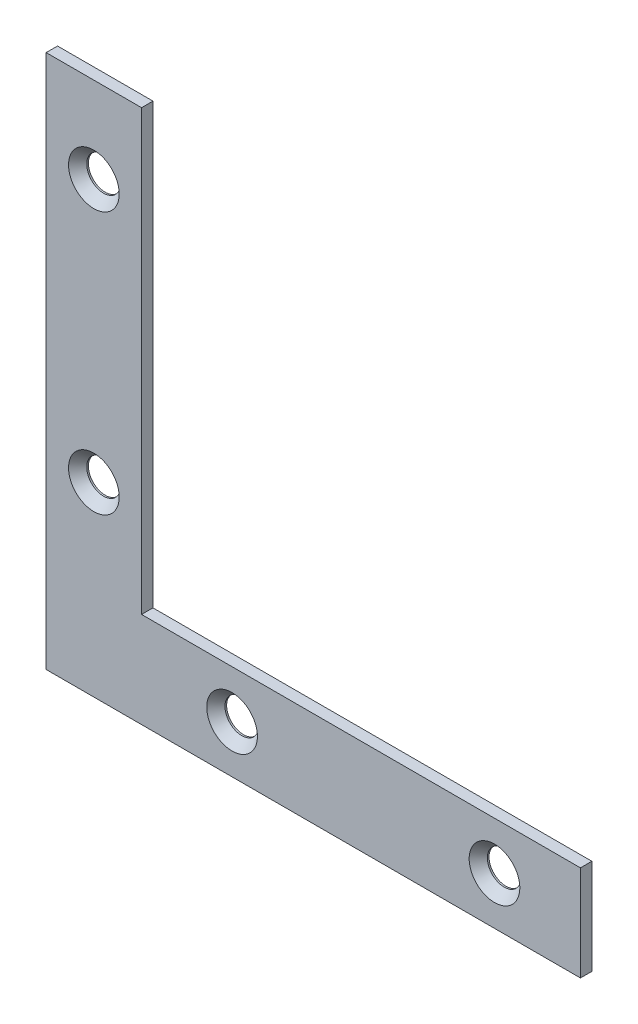
SolidWorks part; units mm, degrees
ref_plane "Front Plane" through (0, 0, 0) normal (0, 0, 1) x (1, 0, 0)
ref_plane "Top Plane" through (0, 0, 0) normal (0, 1, 0) x (1, 0, 0)
ref_plane "Right Plane" through (0, 0, 0) normal (1, 0, 0) x (0, 0, -1)
sketch "Sketch1" plane through (0, 0, 0) normal (0, 0, 1) x (1, 0, 0)
  line L0 (-44.45, 44.45) -> (-44.45, -44.45) construction
  line L1 (-44.45, -44.45) -> (44.45, -44.45) construction
  line L2 (44.45, -44.45) -> (44.45, -28.575) construction
  line L3 (44.45, -28.575) -> (-28.575, -28.575) construction
  line L4 (-28.575, -28.575) -> (-28.575, 44.45) construction
  line L5 (-28.575, 44.45) -> (-44.45, 44.45) construction
  line L6 (-44.45, -44.45) -> (44.45, 44.45) construction
  line L7 (-36.5125, 44.45) -> (-36.5125, -36.5125) construction
  line L8 (-36.5125, -36.5125) -> (44.45, -36.5125) construction
  line L9 (-16.4942, -39.4939) -> (-10.5314, -33.5311) construction
  circle A0 centre (-13.5128, -36.5125) radius 2.8067 construction
  point P10 (-36.5125, -13.5128)
  point P11 (-36.5125, 30.1498)
  point P12 (-13.5128, -36.5125)
  point P13 (30.1498, -36.5125)
  dimension "Hole Size" = 5.6134
  dimension "Length (A)" = 88.9
  dimension "Length (C)" = 88.9
  dimension "Length (B)" = 15.875
  dimension "Hole Spacing (A)" = 43.6626
  dimension "Hole Offset (A)" = 14.3002
  dimension "Hole Offset (C)" = 14.3002
  dimension "Hole Spacing (C)" = 43.6626
  dimension "D1" = 45
  dimension "C'Sink Size" = 8.4328
sketch "Sketch2" plane through (0, 0, 0) normal (1, 0, 0) x (0, 0, -1)
  line L0 (0.9487, 44.45) -> (-0.9487, 44.45)
  dimension "Thickness" = 1.8974
sketch "Sketch3" plane through (0, 0, 0) normal (0, 0, 1) x (1, 0, 0)
  line L0 (-44.45, 44.45) -> (-28.575, 44.45)
  line L1 (-28.575, 44.45) -> (-28.575, -28.575)
  line L2 (-28.575, -28.575) -> (44.45, -28.575)
  line L3 (44.45, -28.575) -> (44.45, -44.45)
  line L4 (44.45, -44.45) -> (-44.45, -44.45)
  line L5 (-44.45, -44.45) -> (-44.45, 44.45)
extrude "Boss-Extrude1" add sketch "Sketch3" along normal up to vertex (0.9487 mm away) and the other way up to vertex (0.9487 mm away) up to point (0, 44.45, 0.9487) other way up to point (0, 44.45, -0.9487)
sketch "Sketch4" plane through (0, 0, 0) normal (0, 0, 1) x (1, 0, 0)
  line L0 (-16.4942, -39.4939) -> (-10.5314, -33.5311) construction
  circle A0 centre (-36.5125, 30.1498) radius 2.8067
  circle A1 centre (-36.5125, -13.5128) radius 2.8067
  circle A2 centre (-13.5128, -36.5125) radius 2.8067
  circle A3 centre (30.1498, -36.5125) radius 2.8067
  circle A4 centre (-13.5128, -36.5125) radius 2.8067 construction
extrude "Cut-Extrude1" cut sketch "Sketch4" against normal through all both and the other way through all
sketch "Sketch5" plane through (0, 0, 0.9487) normal (0, 0, 1) x (1, 0, 0)
  line L0 (-36.5125, 44.45) -> (-36.5125, -36.5125) construction
  line L1 (-16.4942, -39.4939) -> (-10.5314, -33.5311) construction
  circle A0 centre (-36.5125, 30.1498) radius 4.2164
  circle A1 centre (-36.5125, -13.5128) radius 4.2164
  circle A2 centre (-13.5128, -36.5125) radius 4.2164
  circle A3 centre (30.1498, -36.5125) radius 4.2164
extrude "Cut-Extrude2" cut sketch "Sketch5" against normal through all draft 41
sketch "Sketch6" plane through (0, 0, 0.9487) normal (0, 0, 1) x (1, 0, 0)
  line L0 (-36.5125, 44.45) -> (-36.5125, 38.0549)
  line L1 (-28.575, 44.45) -> (-44.45, 44.45) construction
  line L2 (-36.5125, 38.0549) -> (-28.575, 38.0549)
  line L3 (-28.575, -28.575) -> (-28.575, 44.45) construction
  line L4 (-36.5125, -44.45) -> (-36.5125, -35.3911)
  line L5 (-44.45, -44.45) -> (44.45, -44.45) construction
  line L6 (-36.5125, -35.3911) -> (-44.45, -35.3911)
  line L7 (-44.45, 44.45) -> (-44.45, -44.45) construction
  line L8 (44.45, -36.5125) -> (37.2304, -36.5125)
  line L9 (44.45, -44.45) -> (44.45, -28.575) construction
  line L10 (37.2304, -36.5125) -> (37.2304, -44.45)
sketch "Sketch7" plane through (0, 0, -0.9487) normal (0, 0, -1) x (-1, 0, 0)
  line L0 (36.5125, 44.45) -> (36.5125, 34.3763)
  line L1 (28.575, 44.45) -> (44.45, 44.45) construction
  line L2 (36.5125, -36.7864) -> (36.5125, -44.45)
  line L3 (44.45, -44.45) -> (-44.45, -44.45) construction
  line L4 (-36.0888, -36.5125) -> (-44.45, -36.5125)
  line L5 (-44.45, -44.45) -> (-44.45, -28.575) construction
  line L6 (-36.0888, -36.5125) -> (-36.0888, -44.45)
  line L7 (36.5125, -36.7864) -> (44.45, -36.7864)
  line L8 (44.45, 44.45) -> (44.45, -44.45) construction
  line L9 (36.5125, 34.3763) -> (44.45, 34.3763)
equation "\"Hole Spacing (A)@Sketch1\"=\"Hole Spacing (C)@Sketch1\""
equation "\"Hole Offset (A)@Sketch1\"=\"Hole Offset (C)@Sketch1\""
